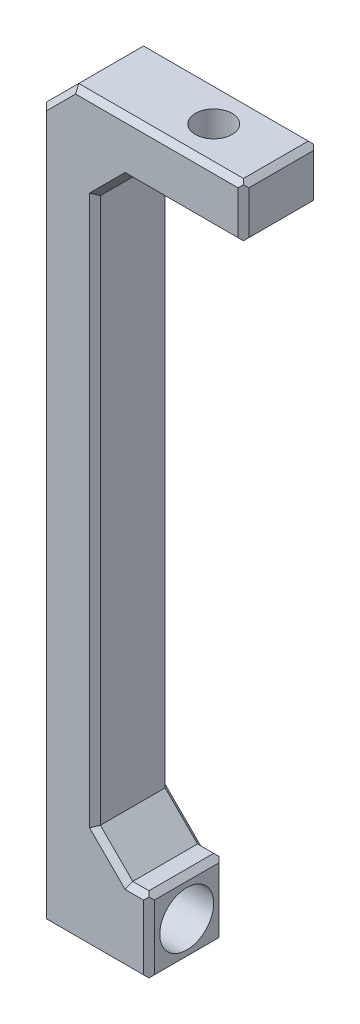
SolidWorks part; units mm, degrees
ref_plane "Alzado" through (0, 0, 0) normal (0, 0, 1) x (1, 0, 0)
ref_plane "Planta" through (0, 0, 0) normal (0, 1, 0) x (1, 0, 0)
ref_plane "Vista lateral" through (0, 0, 0) normal (1, 0, 0) x (0, 0, -1)
sketch "Croquis1" plane through (0, 0, 0) normal (0, 0, 1) x (1, 0, 0)
  line L0 (12.5, 65) -> (12.5, 60)
  line L1 (-2.5, -3.5) -> (-2.5, 3.5)
  line L2 (-2.5, -3.5) -> (-12.5, -3.5)
  line L3 (-2.5, 3.5) -> (-7.5, 3.5)
  line L4 (0, -1000) -> (0, 49000) construction
  line L5 (-7.5, 3.5) -> (-7.5, 60)
  line L6 (-12.5, 3.5) -> (-12.5, 65)
  line L7 (-7.5, 60) -> (0, 60)
  line L8 (-12.5, 65) -> (0, 65)
  line L9 (-12.5, 3.5) -> (-12.5, -3.5)
  line L15 (12.5, 65) -> (0, 65)
  line L16 (7.5, 60) -> (0, 60)
  line L18 (7.5, 60) -> (12.5, 60)
  line L19 (6.25, 65) -> (6.25, 60)
  point P4 (0, 0)
  point P8 (-2.5, 0)
  dimension "D1" = 60
  dimension "D2" = 7
  dimension "D3" = 2.5
  dimension "D4" = 5
  dimension "D5" = 5
extrude "Saliente-Extruir1" add sketch "Croquis1" along normal mid plane 7 contours L7 L4 L8 L6 L9 L2 L1 L3 L5 | L4 L16 L19 L15
sketch "Croquis2" plane through (0, 0, 0) normal (1, 0, 0) x (0, 0, -1)
  circle A0 centre (0, 0) radius 2.5
  dimension "D1" = 5
extrude "Cortar-Extruir1" cut sketch "Croquis2" against normal through all both and the other way through all
hole_wizard "Taladro de margen para M31" positions "Croquis4" profile "Croquis6" hole size "M3" standard "Ansi Metric" end condition through all
sketch "Croquis4" plane through (0, 65, 0) normal (0, 1, 0) x (1, 0, 0)
  point P0 (0, 0)
sketch "Croquis6" plane through (0, 65, 0) normal (1, 0, 0) x (0, 0, 1)
  line L0 (0, 0) -> (0, 68.5)
  line L1 (0, 68.5) -> (1.7, 68.5)
  line L2 (1.7, 68.5) -> (1.7, 0)
  line L5 (1.7, 0) -> (0, 0)
  line L11 (0, -6.35) -> (0, 107.95) construction
  dimension "Diámetro de taladro hasta el siguiente" = 3.4
  dimension "Profundidad de taladro hasta el siguiente" = 68.5
chamfer "Chaflán1" distance 3 angle 45 3 edges at (-7.5, 3.5, 0) (-12.5, 65, 0) (-7.5, 60, 0)
chamfer "Chaflán2" distance 0.5 angle 45 22 edges at (-7.5, -3.5, -3.5) (-7.5, -3.5, 3.5) (-2.5, 0, -3.5) (-2.5, 0, 3.5) (-3.5, 3.5, -3.5) (-3.5, 3.5, 3.5) (-6, 5, 3.5) (-6, 5, -3.5) (-7.5, 31.75, 3.5) (-7.5, 31.75, -3.5) (-6, 58.5, 3.5) (-6, 58.5, -3.5) (0.875, 60, 3.5) (0.875, 60, -3.5) (6.25, 62.5, -3.5) (6.25, 62.5, 3.5) (-1.625, 65, -3.5) (-1.625, 65, 3.5) (-11, 63.5, 3.5) (-11, 63.5, -3.5) (-12.5, 29.25, 3.5) (-12.5, 29.25, -3.5)
chamfer "Chaflán3" distance 0.5 angle 45 5 edges at (-12.5, -3.5, 0) (-2.5, -3.5, 0) (-2.5, 3.5, 0) (6.25, 65, 0) (6.25, 60, 0)
